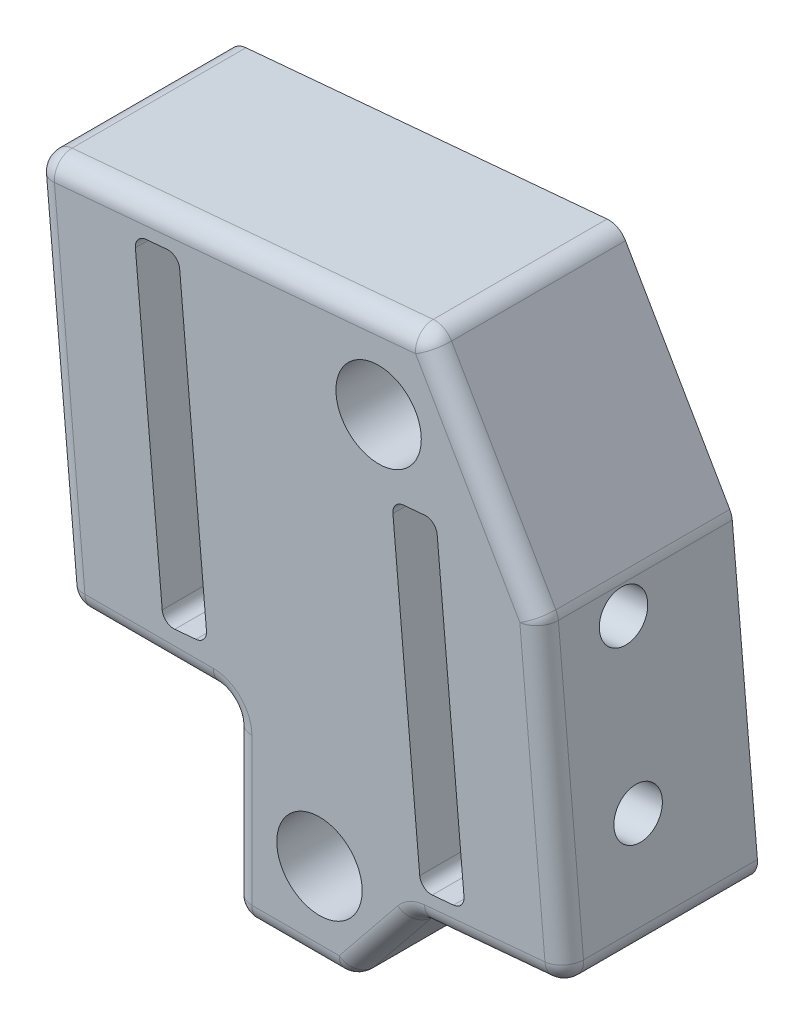
SolidWorks part; units mm, degrees
ref_plane "Front Plane" through (0, 0, 0) normal (0, 0, 1) x (1, 0, 0)
ref_plane "Top Plane" through (0, 0, 0) normal (0, 1, 0) x (1, 0, 0)
ref_plane "Right Plane" through (0, 0, 0) normal (1, 0, 0) x (0, 0, -1)
sketch "Sketch1" plane through (0, 0, 0) normal (0, 0, 1) x (1, 0, 0)
  line L0 (19.2475, -20.5544) -> (17.4577, -0.5105)
  line L1 (17.4577, -0.5105) -> (10.0597, 12.3033)
  line L2 (-15.7519, 9.9985) -> (10.0597, 12.3033)
  line L3 (-15.7519, 9.9985) -> (-13.532, -14.8636)
  line L4 (-13.532, -14.8636) -> (-2.667, -14.8636)
  line L5 (-2.667, -14.8636) -> (-2.667, -27.0806)
  line L6 (-2.667, -27.0806) -> (4.953, -27.0806)
  line L7 (19.2475, -20.5544) -> (9.525, -21.4225)
  line L8 (4.953, -27.0806) -> (19.2475, -20.5544) construction
  line L9 (24.4247, -11.5616) -> (15.5347, 3.8363) construction
  line L10 (18.711, -14.5458) -> (18.4851, -12.0158) construction
  line L11 (-22.225, -15.3716) -> (-4.445, -15.3716) construction
  line L12 (-3.175, -16.6416) -> (-3.175, -25.8106) construction
  line L13 (-14.2553, -6.7623) -> (-14.0294, -9.2922) construction
  line L14 (-4.445, -27.0806) -> (-8.8646, -27.0806) construction
  line L15 (9.525, -21.4225) -> (4.953, -27.0806)
  line L17 (8.255, -29.1126) -> (8.255, -26.5726) construction
  line L21 (0.2522, 5.6898) -> (-14.9274, 4.3344) construction
  line L28 (-8.5213, 8.0941) -> (-8.8217, 8.0673) construction
  line L30 (12.0168, -18.6499) -> (12.3173, -18.6231) construction
  dimension "D1" = 0.508
  dimension "D2" = 0.508
  dimension "D3" = 0.508
  dimension "D4" = 2.54
  dimension "D5" = 7.62
  dimension "D6" = 2.54
  dimension "D7" = 1.27
extrude "Boss-Extrude1" add sketch "Sketch1" along normal blind 12.7 contours L0 L1 L2 L3 L4 L5 L6 L15 L7
fillet "Fillet1" radius 1.27 18 edges at (-2.667, -20.9721, 12.7) (-8.0995, -14.8636, 12.7) (-14.642, -2.4325, 12.7) (-2.8461, 11.1509, 12.7) (13.7587, 5.8964, 12.7) (18.3526, -10.5324, 12.7) (1.143, -27.0806, 12.7) (-2.667, -27.0806, 6.35) (17.4577, -0.5105, 6.35) (10.0597, 12.3033, 6.35) (-15.7519, 9.9985, 6.35) (-13.532, -14.8636, 6.35) (-2.667, -14.8636, 6.35) (7.239, -24.2516, 12.7) (14.3863, -20.9884, 12.7) (19.2475, -20.5544, 6.35) (9.525, -21.4225, 6.35) (4.953, -27.0806, 6.35)
sketch "Sketch2" plane through (0, 0, 12.7) normal (0, 0, 1) x (1, 0, 0)
  line L0 (-8.8217, 8.0673) -> (-6.4183, 8.2819) construction
  line L1 (-8.8217, 8.0673) -> (-7.0145, -12.1722) construction
  line L2 (-6.4183, 8.2819) -> (-4.6111, -11.9576) construction
  line L3 (-7.0145, -12.1722) -> (-4.6111, -11.9576) construction
  line L4 (-4.9115, -11.9844) -> (-4.6111, -11.9576) construction
  line L5 (8.1066, 1.4018) -> (10.5101, 1.6164) construction
  line L6 (8.1066, 1.4018) -> (9.9138, -18.8377) construction
  line L7 (10.5101, 1.6164) -> (12.3173, -18.6231) construction
  line L8 (9.9138, -18.8377) -> (12.3173, -18.6231) construction
  line L9 (-9.1199, 8.5507) -> (-6.2105, 8.8104)
  line L10 (-9.1199, 8.5507) -> (-7.2223, -12.7008)
  line L11 (-6.2105, 8.8104) -> (-4.3129, -12.441)
  line L12 (-7.2223, -12.7008) -> (-4.3129, -12.441)
  line L13 (7.8084, 1.8852) -> (10.7179, 2.145)
  line L14 (7.8084, 1.8852) -> (9.706, -19.3662)
  line L15 (10.7179, 2.145) -> (12.6154, -19.1065)
  line L16 (9.706, -19.3662) -> (12.6154, -19.1065)
  line L17 (12.0168, -18.6499) -> (12.3173, -18.6231) construction
  dimension "D1" = 0.508
  dimension "D2" = 0.508
  dimension "D3" = 0.254
  dimension "D4" = 0.254
  dimension "D5" = 0.508
  dimension "D6" = 0.508
  dimension "D7" = 0.254
  dimension "D8" = 0.254
extrude "Cut-Extrude1" cut sketch "Sketch2" against normal through all
fillet "Fillet2" radius 0.762 8 edges at (7.8084, 1.8852, 6.35) (10.7179, 2.145, 6.35) (12.6154, -19.1065, 6.35) (9.706, -19.3662, 6.35) (-4.3129, -12.441, 6.35) (-7.2223, -12.7008, 6.35) (-6.2105, 8.8104, 6.35) (-9.1199, 8.5507, 6.35)
hole_wizard "1/8 (0.1250) Dowel Hole1" positions "3DSketch1" profile "Sketch4" hole size "1/8" standard "ANSI Inch"
sketch3d "3DSketch1"
  circle A0 centre (-15.1025, 2.725, 7.3025) radius 1.27 construction
  circle A1 centre (-14.1424, -8.0272, 7.3025) radius 1.27 construction
  circle A2 centre (17.6379, -2.5286, 7.3025) radius 1.27 construction
  circle A3 centre (18.598, -13.2808, 7.3025) radius 1.27 construction
  point P0 (17.6379, -2.5286, 7.3025)
  point P2 (18.598, -13.2808, 7.3025)
  point P4 (-15.1025, 2.725, 7.3025)
  point P6 (-14.1424, -8.0272, 7.3025)
  point P13 (-16.3674, 2.612, 7.3025)
  point P18 (-15.4074, -8.1402, 7.3025)
  point P22 (18.9029, -2.4156, 7.3025)
  point P27 (19.863, -13.1678, 7.3025)
sketch "Sketch4" plane through (17.6379, -2.5286, 7.3025) normal (0, 0, 1) x (-0.0889, 0.996, 0)
  line L0 (0, 0) -> (0, 16.8289)
  line L1 (0, 16.8289) -> (1.5875, 15.875)
  line L2 (1.5875, 15.875) -> (1.5875, 0)
  line L5 (1.5875, 0) -> (0, 0)
  line L10 (0, 16.8289) -> (-1.5875, 15.875) construction
  line L11 (0, -6.35) -> (0, 107.95) construction
  dimension "Hole Dia." = 3.175
  dimension "Hole Depth" = 15.875
  dimension "Drill Angle" = 118
hole_wizard "#8 Clearance Hole1" positions "Sketch5" profile "Sketch6" hole size "#8" standard "ANSI Inch"
sketch "Sketch5" plane through (0, 0, 12.7) normal (0, 0, 1) x (1, 0, 0)
  line L0 (6.9344, 6.2865) -> (10.7839, 8.509)
  line L1 (16.2177, -0.9027) -> (9.3652, 10.9662) construction
  line L3 (6.9344, 6.2865) -> (6.5391, 10.7139)
  line L4 (9.3652, 10.9662) -> (-14.374, 8.8465) construction
  line L6 (3.048, -25.8106) -> (3.048, -21.3656)
  line L7 (-1.397, -25.8106) -> (4.3464, -25.8106) construction
  line L8 (3.048, -21.3656) -> (-1.397, -21.3656)
  line L9 (-1.397, -16.1336) -> (-1.397, -25.8106) construction
  point P0 (6.9344, 6.2865)
  point P2 (3.048, -21.3656)
  dimension "D1" = 4.445
  dimension "D2" = 4.445
sketch "Sketch6" plane through (6.9344, 6.2865, 12.7) normal (1, 0, 0) x (0, -1, 0)
  line L0 (0, 0) -> (0, 17.3527)
  line L1 (0, 17.3527) -> (2.2479, 16.002)
  line L2 (2.2479, 16.002) -> (2.2479, 0)
  line L5 (2.2479, 0) -> (0, 0)
  line L10 (0, 17.3527) -> (-2.2479, 16.002) construction
  line L11 (0, -6.35) -> (0, 107.95) construction
  dimension "Hole Dia." = 4.4958
  dimension "Hole Depth" = 16.002
  dimension "Drill Angle" = 118
hole_wizard "#2 (0.221) Diameter Hole1" positions "Sketch7" profile "Sketch8" hole size "#2" standard "ANSI Inch"
sketch "Sketch7" plane through (0, 0, 12.7) normal (0, 0, 1) x (1, 0, 0)
  point P0 (6.9344, 6.2865)
  point P3 (3.048, -21.3656)
sketch "Sketch8" plane through (6.9344, 6.2865, 12.7) normal (1, 0, 0) x (0, -1, 0)
  line L0 (0, 0) -> (0, 6.3854)
  line L1 (0, 6.3854) -> (2.8067, 4.699)
  line L2 (2.8067, 4.699) -> (2.8067, 0)
  line L5 (2.8067, 0) -> (0, 0)
  line L10 (0, 6.3854) -> (-2.8067, 4.699) construction
  line L11 (0, -6.35) -> (0, 107.95) construction
  dimension "Hole Dia." = 5.6134
  dimension "Hole Depth" = 4.699
  dimension "Drill Angle" = 118
equation "\"D2@Sketch1\"=\"D1@Sketch1\""
equation "\"D3@Sketch1\"=\"D1@Sketch1\""
equation "\"D6@Sketch1\"=\"D4@Sketch1\""
equation "\"D4@Sketch2\"=\"D3@Sketch2\""
equation "\"D2@Sketch2\"=\"D1@Sketch2\""
equation "\"D5@Sketch2\"=\"D1@Sketch2\""
equation "\"D6@Sketch2\"=\"D1@Sketch2\""
equation "\"D7@Sketch2\"=\"D3@Sketch2\""
equation "\"D8@Sketch2\"=\"D4@Sketch2\""
